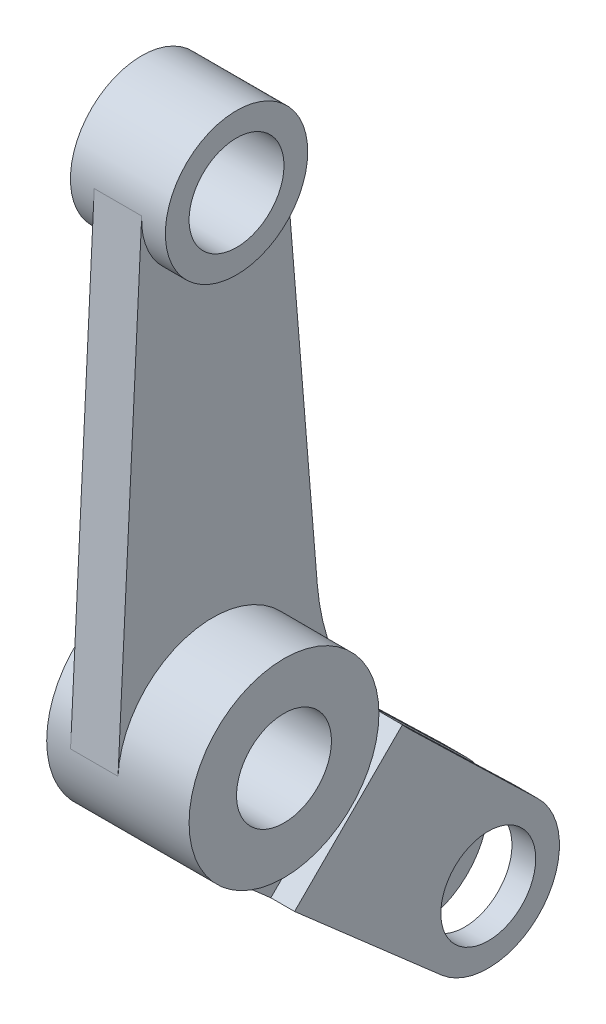
SolidWorks part; units mm, degrees
ref_plane "Ön Düzlem" through (0, 0, 0) normal (0, 0, 1) x (1, 0, 0)
ref_plane "Üst Düzlem" through (0, 0, 0) normal (0, 1, 0) x (1, 0, 0)
ref_plane "Sağ Düzlem" through (0, 0, 0) normal (1, 0, 0) x (0, 0, -1)
sketch "Çizim1" plane through (0, 0, 0) normal (1, 0, 0) x (0, 0, -1)
  line L0 (0, 0) -> (41.4848, 0) construction
  line L1 (0, 0) -> (0, 100) construction
  line L2 (0, 0) -> (53.033, -53.033) construction
  line L3 (14.9499, 101.2249) -> (22.0049, 15.1163)
  line L4 (37.0829, -16.7464) -> (63.4595, -42.2493)
  line L5 (-14.9812, 100.75) -> (-19.975, 1)
  line L6 (-13.1679, -15.0535) -> (43.1571, -64.3231)
  arc A0 (14.9499, 101.2249) -> (-14.9812, 100.75) centre (0, 100) ccw
  circle A1 centre (0, 0) radius 20
  arc A2 (43.1571, -64.3231) -> (63.4595, -42.2493) centre (53.033, -53.033) ccw
  arc A3 (37.0829, -16.7464) -> (22.0049, 15.1163) centre (71.838, 19.1992) cw
  dimension "D1" = 45
  dimension "D2" = 30
  dimension "D3" = 40
  dimension "D4" = 30
  dimension "D7" = 50
  dimension "D5" = 75
  dimension "D6" = 100
extrude "Yükseklik-Ekstrüzyon1" add sketch "Çizim1" along normal blind 10 contours L4 A3 L3 A0 L5 A1 L6 A2 | A1
sketch "Çizim2" plane through (10, 0, 0) normal (1, 0, 0) x (0, 0, -1)
  circle A0 centre (0, 100) radius 15
  dimension "D1" = 30
extrude "Yükseklik-Ekstrüzyon2" add sketch "Çizim2" along normal blind 5
ref_plane "Düzlem1" through (5, 0, 0) normal (1, 0, 0) x (0, 0, -1)
mirror "Aynalama1" about plane through (5, 0, 0) normal (1, 0, 0) of "Yükseklik-Ekstrüzyon2"
sketch "Çizim3" plane through (10, 0, 0) normal (1, 0, 0) x (0, 0, -1)
  circle A0 centre (0, 0) radius 20
  dimension "D1" = 40
extrude "Yükseklik-Ekstrüzyon3" add sketch "Çizim3" along normal blind 15
sketch "Çizim4" plane through (0, 0, 0) normal (-1, 0, 0) x (0, 0, 1)
  circle A0 centre (0, 0) radius 20
  dimension "D1" = 40
extrude "Yükseklik-Ekstrüzyon4" add sketch "Çizim4" along normal blind 5
sketch "Çizim5" plane through (15, 0, 0) normal (1, 0, 0) x (0, 0, -1)
  circle A0 centre (0, 100) radius 10
  circle A1 centre (0, 0) radius 10
  dimension "D1" = 20
  dimension "D2" = 20
extrude "Kes-Ekstrüzyon1" cut sketch "Çizim5" against normal through all both and the other way through all
sketch "Çizim6" plane through (10, 0, 0) normal (1, 0, 0) x (0, 0, -1)
  line L0 (0, 0) -> (53.033, -53.033) construction
  line L1 (34.9469, -14.5506) -> (12.2287, -37.2688)
  line L2 (-13.1679, -15.0535) -> (43.1571, -64.3231) construction
  line L7 (-14.9812, 100.75) -> (-19.975, 1)
  line L8 (-13.1679, -15.0535) -> (43.1571, -64.3231)
  line L9 (63.4595, -42.2493) -> (37.0829, -16.7464)
  line L10 (22.0049, 15.1163) -> (14.9499, 101.2249)
  arc A0 (22.0049, 15.1163) -> (37.0829, -16.7464) centre (71.838, 19.1992) ccw construction
  arc A5 (-13.1679, -15.0535) -> (-19.975, 1) centre (0, 0) ccw
  arc A6 (43.1571, -64.3231) -> (63.4595, -42.2493) centre (53.033, -53.033) ccw
  arc A7 (22.0049, 15.1163) -> (37.0829, -16.7464) centre (71.838, 19.1992) ccw
  arc A8 (-14.9812, 100.75) -> (14.9499, 101.2249) centre (0, 100) ccw
  arc A10 (43.1571, -64.3231) -> (63.4595, -42.2493) centre (53.033, -53.033) ccw
  dimension "D1" = 40
  dimension "D2" = 0
extrude "Yükseklik-Ekstrüzyon5" add sketch "Çizim6" along normal blind 5
mirror "Aynalama2" about plane through (5, 0, 0) normal (1, 0, 0) of "Yükseklik-Ekstrüzyon5"
ref_plane "Düzlem2" through (0, -24.7487, -24.7487) normal (0, 0.7071, 0.7071) x (1, 0, 0)
sketch "Çizim8" plane through (0, -24.7487, -24.7487) normal (0, 0.7071, 0.7071) x (1, 0, 0)
  line L0 (10, 60.6477) -> (10, -13.4173) construction
  line L1 (0, -33.4935) -> (10, -33.4935)
  line L2 (0, -33.4935) -> (0, 21.9735)
  line L3 (0, 21.9735) -> (10, 21.9735)
  line L4 (10, -33.4935) -> (10, 21.9735)
extrude "Kes-Ekstrüzyon3" cut sketch "Çizim8" against normal blind 90 from offset 5 offset against normal yes
sketch "Çizim9" plane through (15, 0, 0) normal (1, 0, 0) x (0, 0, -1)
  circle A0 centre (53.033, -53.033) radius 10
  dimension "D1" = 20
extrude "Kes-Ekstrüzyon4" cut sketch "Çizim9" against normal through all
